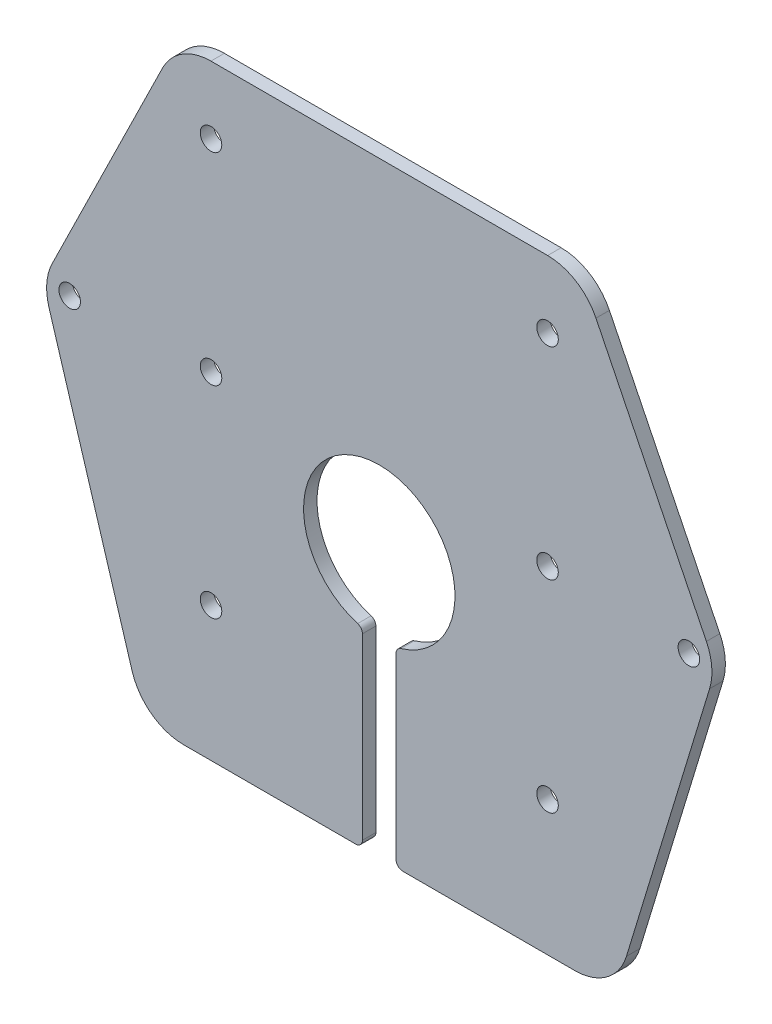
SolidWorks part; units mm, degrees
material "环氧板3240"
ref_plane "前视基准面" through (0, 0, 0) normal (0, 0, 1) x (1, 0, 0)
ref_plane "上视基准面" through (0, 0, 0) normal (0, 1, 0) x (1, 0, 0)
ref_plane "右视基准面" through (0, 0, 0) normal (1, 0, 0) x (0, 0, -1)
other "Configuration Table"
sketch "草图1" plane through (0, 0, 0) normal (0, 0, 1) x (1, 0, 0)
  line L0 (-30, 0) -> (30, 0)
  line L1 (30, 0) -> (50, -40.7)
  line L2 (50, -40.7) -> (35, -90)
  line L3 (35, -90) -> (-35, -90)
  line L4 (0, -90) -> (0, 0) construction
  line L5 (-50, -40.7) -> (-35, -90)
  line L6 (-30, 0) -> (-50, -40.7)
  line L7 (-25, -10) -> (25, -10) construction
  line L8 (-50, -40.7) -> (50, -40.7) construction
  line L9 (25, -10) -> (25, -40) construction
  line L10 (25, -40) -> (-25, -40) construction
  line L11 (-25, -70) -> (25, -70) construction
  line L12 (25, -40) -> (25, -70) construction
  circle A0 centre (-25, -10) radius 1.6
  circle A1 centre (-46, -40.7) radius 1.6
  circle A2 centre (25, -10) radius 1.6
  circle A3 centre (46, -40.7) radius 1.6
  circle A4 centre (-25, -10) radius 4 construction
  circle A5 centre (-46, -40.7) radius 4 construction
  circle A6 centre (-25, -40) radius 1.6
  circle A7 centre (25, -40) radius 1.6
  circle A8 centre (-25, -70) radius 1.6
  circle A9 centre (25, -70) radius 1.6
  dimension "D5" = 3.2
  dimension "D9" = 8
  dimension "D10" = 8
  dimension "D1" = 60
  dimension "D2" = 70
  dimension "D3" = 90
  dimension "D4" = 100
  dimension "D6" = 50
  dimension "D7" = 92
  dimension "D8" = 10
  dimension "D11" = 40.7
  dimension "D12" = 30
  dimension "D13" = 30
extrude "凸台-拉伸1" add sketch "草图1" along normal blind 2
fillet "圆角1" radius 8 6 edges at (30, 0, 1) (-30, 0, 1) (50, -40.7, 1) (-50, -40.7, 1) (35, -90, 1) (-35, -90, 1)
sketch "草图2" plane through (0, 0, 2) normal (0, 0, 1) x (1, 0, 0)
  line L0 (0, 0) -> (0, -90) construction
  line L1 (-29.072, -90) -> (29.072, -90) construction
  line L2 (25.0175, 0) -> (-25.0175, 0) construction
  line L3 (-2.5, -90) -> (2.5, -90)
  line L4 (14.4338, -50.7) -> (7.2169, -38.2) construction
  line L5 (7.2169, -38.2) -> (-7.2169, -38.2) construction
  line L6 (-7.2169, -38.2) -> (-14.4338, -50.7) construction
  line L7 (-14.4338, -50.7) -> (-7.2169, -63.2) construction
  line L8 (-7.2169, -63.2) -> (7.2169, -63.2) construction
  line L9 (7.2169, -63.2) -> (14.4338, -50.7) construction
  line L10 (-2.5, -90) -> (-2.5, -61.6687)
  line L11 (-2.5, -61.6687) -> (2.5, -61.6687)
  line L12 (2.5, -90) -> (2.5, -61.6687)
  circle A0 centre (0, -50.7) radius 11.25
  circle A1 centre (0, -50.7) radius 12.5 construction
  line M8 (-29.072, -90) -> (29.072, -90)
  dimension "D1" = 22.5
  dimension "D2" = 25
  dimension "D3" = 50.7
  dimension "D4" = 5
extrude "切除-拉伸1" cut sketch "草图2" against normal blind 10 contours A0 L10 L12 M8
fillet "圆角2" radius 1 4 edges at (2.5, -61.6687, 1) (-2.5, -61.6687, 1) (2.5, -90, 1) (-2.5, -90, 1)
sketch "草图3" plane through (0, 0, 2) normal (0, 0, 1) x (1, 0, 0)
  line L0 (-25, -10) -> (-25, -70) construction
  line L1 (0, -50.7) -> (0, 0) construction
  circle A0 centre (-25, -55.7) radius 1.6
  circle A1 centre (-46, -40.7) radius 1.6 construction
  circle A2 centre (25, -55.7) radius 1.6
  circle A3 centre (-25, -15.7) radius 1.6
  circle A4 centre (25, -15.7) radius 1.6
  dimension "D1" = 15
  dimension "D2" = 3.2
  dimension "D3" = 40
extrude "切除-拉伸2" [suppressed] cut sketch "草图3" against normal blind 10
